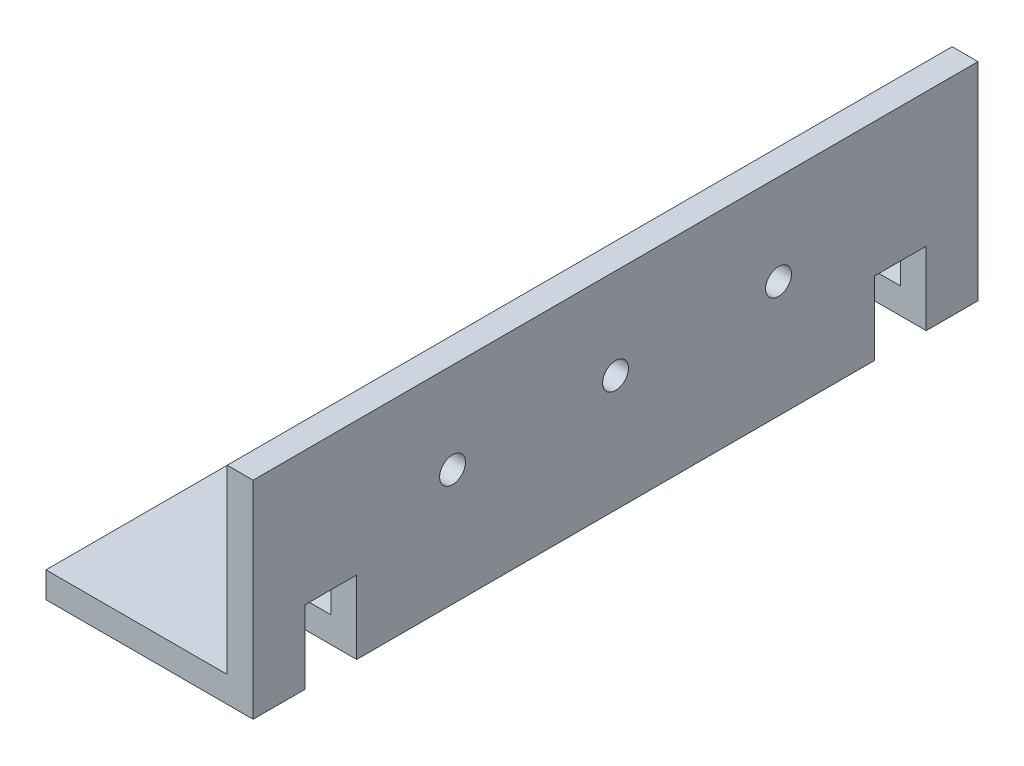
SolidWorks part; units mm, degrees
material "1060 Alloy"
ref_plane "Front Plane" through (0, 0, 0) normal (0, 0, 1) x (1, 0, 0)
ref_plane "Top Plane" through (0, 0, 0) normal (0, 1, 0) x (1, 0, 0)
ref_plane "Right Plane" through (0, 0, 0) normal (1, 0, 0) x (0, 0, -1)
sketch "Sketch1" plane through (0, 0, 0) normal (0, 0, 1) x (1, 0, 0)
  line L0 (0, 0) -> (0, 25.4)
  line L1 (0, 25.4) -> (-3.175, 25.4)
  line L2 (-3.175, 25.4) -> (-3.175, 3.175)
  line L3 (-3.175, 3.175) -> (-25.4, 3.175)
  line L4 (-25.4, 3.175) -> (-25.4, 0)
  line L5 (-25.4, 0) -> (0, 0)
  dimension "D1" = 25.4
  dimension "D2" = 3.175
extrude "Boss-Extrude1" add sketch "Sketch1" along normal blind 88.9
ref_plane "Plane1" through (0, 0, 0) normal (0.7071, 0.7071, 0) x (0, 0, -1)
sketch "Sketch2" plane through (0, 0, 0) normal (0.7071, 0.7071, 0) x (0, 0, -1)
  line L5 (-88.9, 0) -> (0, 0) construction
  line L6 (-82.55, 0) -> (-76.2, 0)
  line L7 (-82.55, 0) -> (-82.55, 6.35)
  line L8 (-82.55, 6.35) -> (-76.2, 6.35)
  line L9 (-76.2, 0) -> (-76.2, 6.35)
  line L10 (-88.9, 0) -> (-82.55, 0) construction
  line L11 (-6.35, 0) -> (-12.7, 0)
  line L12 (-6.35, 0) -> (-6.35, 6.35)
  line L13 (-6.35, 6.35) -> (-12.7, 6.35)
  line L14 (-12.7, 0) -> (-12.7, 6.35)
  line L15 (-6.35, 0) -> (0, 0) construction
  dimension "D1" = 6.35
extrude "Cut-Extrude4" cut sketch "Sketch2" against normal through all both and the other way through all
sketch "Sketch3" plane through (-3.175, 0, 0) normal (-1, 0, 0) x (0, 0, 1)
  line L0 (88.9, 14.2875) -> (0, 14.2875) construction
  line L1 (0, 25.4) -> (0, 3.175) construction
  line L2 (88.9, 25.4) -> (88.9, 3.175) construction
  line L3 (64.4398, 14.2875) -> (24.4602, 14.2875) construction
  circle A0 centre (44.45, 14.2875) radius 1.5875
  circle A1 centre (24.4602, 14.2875) radius 1.5875
  circle A2 centre (64.4398, 14.2875) radius 1.5875
  point P5 (44.45, 14.2875)
  point P12 (0, 14.2875)
  point P16 (44.45, 14.2875)
  dimension "D1" = 3.175
  dimension "D2" = 19.9898
extrude "Cut-Extrude5" cut sketch "Sketch3" against normal through all
